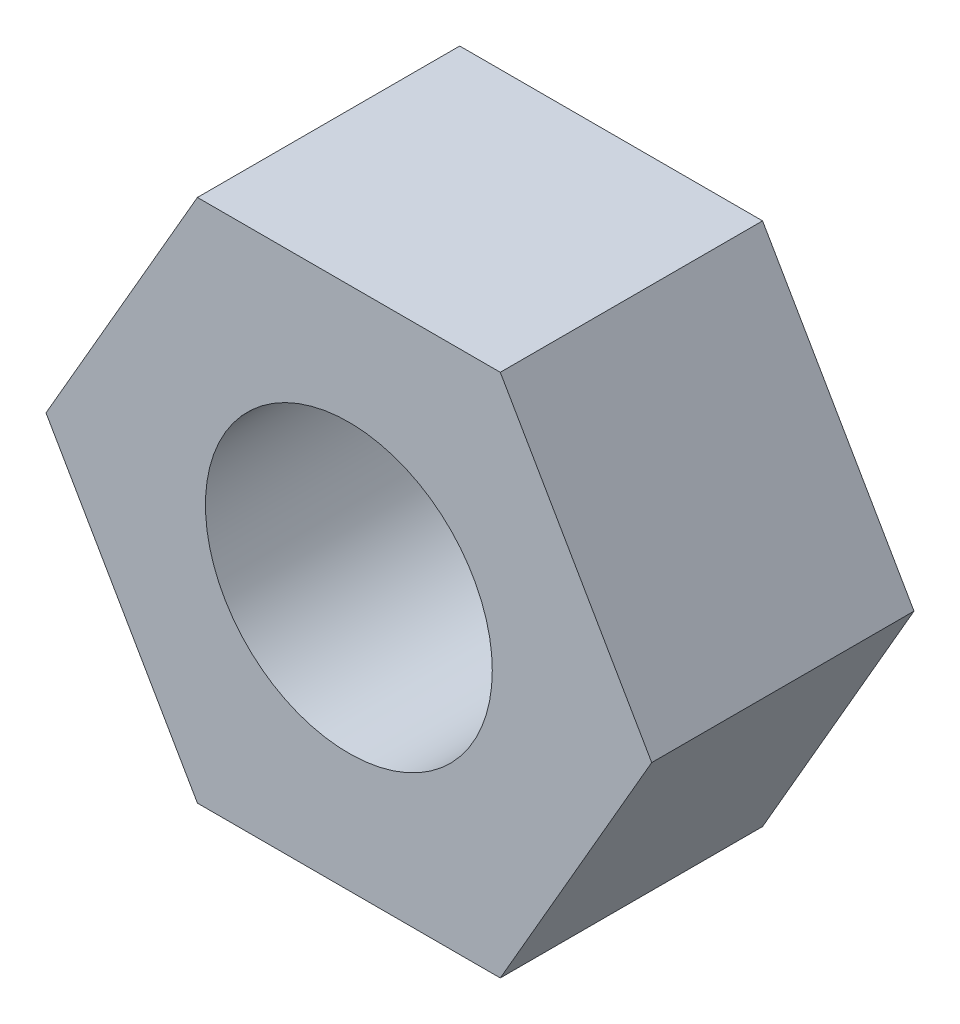
SolidWorks part; units mm, degrees
ref_plane "Front Plane" through (0, 0, 0) normal (0, 0, 1) x (1, 0, 0)
ref_plane "Top Plane" through (0, 0, 0) normal (0, 1, 0) x (1, 0, 0)
ref_plane "Right Plane" through (0, 0, 0) normal (1, 0, 0) x (0, 0, -1)
sketch "Sketch1" plane through (0, 0, 0) normal (0, 0, 1) x (1, 0, 0)
  line L1 (7.3901, 0) -> (3.695, 6.4)
  line L2 (3.695, 6.4) -> (-3.695, 6.4)
  line L3 (-3.695, 6.4) -> (-7.3901, 0)
  line L4 (-7.3901, 0) -> (-3.695, -6.4)
  line L5 (-3.695, -6.4) -> (3.695, -6.4)
  line L6 (3.695, -6.4) -> (7.3901, 0)
  circle A0 centre (0, 0) radius 6.4 construction
  dimension "D1" = 12.8
extrude "Extrude1" add sketch "Sketch1" along normal blind 6.4
hole_wizard "M8x1.0 Tapped Hole1" positions "Sketch3" profile "Sketch4" tap size "M8x1.0" standard "Ansi Metric" end condition through all
sketch "Sketch3" plane through (0, 0, 6.4) normal (0, 0, 1) x (1, 0, 0)
  point P1 (0, 0)
sketch "Sketch4" plane through (0, 0, 6.4) normal (1, 0, 0) x (0, -1, 0)
  line L0 (0, 0) -> (0, 6.4)
  line L1 (0, 6.4) -> (3.5, 6.4)
  line L2 (3.5, 6.4) -> (3.5, 0)
  line L5 (3.5, 0) -> (0, 0)
  line L11 (0, -6.35) -> (0, 107.95) construction
  dimension "Thru Tap Drill Dia." = 7
  dimension "Thru Tap Drill Depth" = 6.4
cosmetic thread "Hole Thread1" parameters "D2"=8
